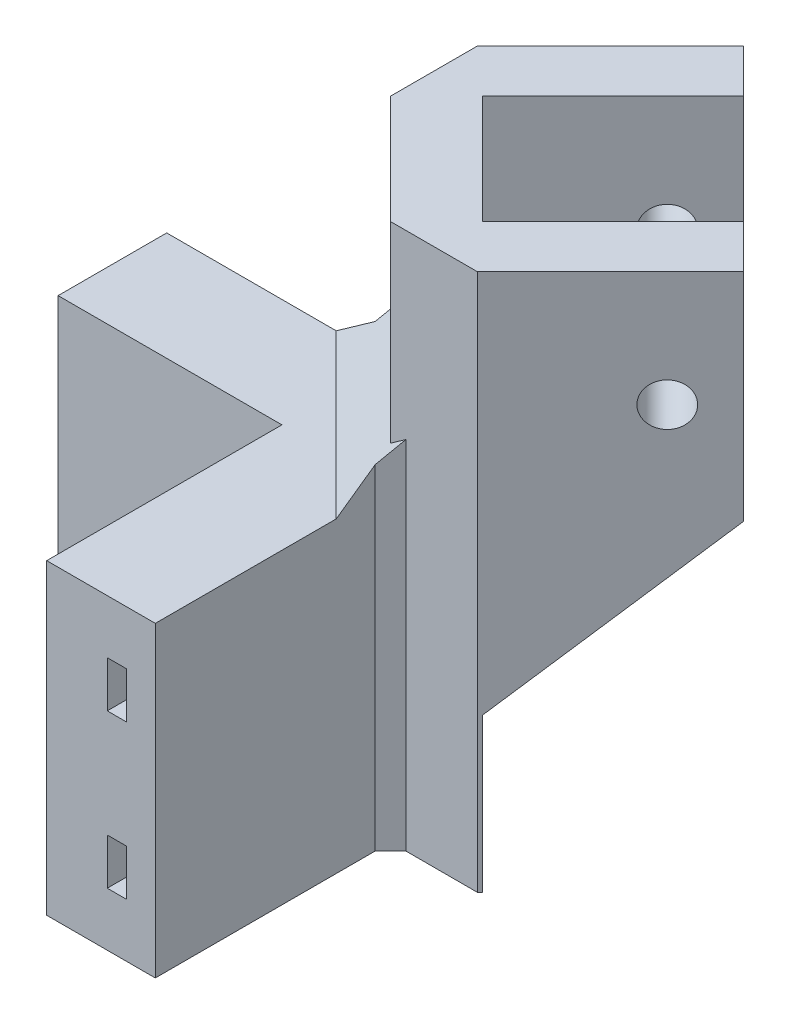
SolidWorks part; units mm, degrees
material "ABS"
ref_plane "Front Plane" through (0, 0, 0) normal (0, 0, 1) x (1, 0, 0)
ref_plane "Top Plane" through (0, 0, 0) normal (0, 1, 0) x (1, 0, 0)
ref_plane "Right Plane" through (0, 0, 0) normal (1, 0, 0) x (0, 0, -1)
sketch "Sketch1" plane through (0, 0, 0) normal (0, 1, 0) x (1, 0, 0)
  line L0 (-75, -75) -> (-25, -75) construction
  line L1 (-75, 75) -> (75, 75) construction
  line L2 (-75, 75) -> (-75, -75) construction
  line L3 (-75, -75) -> (75, -75) construction
  line L4 (75, 75) -> (75, -75) construction
  line L5 (-75, 75) -> (75, -75) construction
  line L6 (-75, -75) -> (75, 75) construction
  line L7 (-25, -75) -> (-25, -25) construction
  line L8 (-25, -25) -> (-75, -25) construction
  line L9 (-75, -25) -> (-75, -75) construction
  line L10 (-75, -60.8579) -> (-39.1421, -25) construction
  line L11 (-39.1421, -25) -> (-25, -39.1421) construction
  line L12 (-25, -39.1421) -> (-60.8579, -75) construction
  line L13 (-60.8579, -75) -> (-75, -60.8579) construction
  line L14 (-69, -54.8579) -> (-54.8579, -69)
  line L15 (-54.8579, -69) -> (-39.3015, -53.4437)
  line L23 (-53.4437, -39.3015) -> (-59.1005, -33.6447)
  line L24 (-59.1005, -33.6447) -> (-75, -49.5442)
  line L25 (-75, -49.5442) -> (-75, -75)
  line L26 (-39.3015, -53.4437) -> (-33.6447, -59.1005)
  line L27 (-33.6447, -59.1005) -> (-49.5442, -75)
  line L28 (-49.5442, -75) -> (-75, -75)
  line L29 (-69, -54.8579) -> (-53.4437, -39.3015)
  point P0 (0, 0)
  dimension "D1" = 150
  dimension "D2" = 150
  dimension "D3" = 50
  dimension "D4" = 20
  dimension "D5" = 22
  dimension "D6" = 6
  dimension "D7" = 8
extrude "Boss-Extrude1" add sketch "Sketch1" along normal blind 30 contours L27 L28 L25 L24 L23 L29 L14 L15 L26
sketch "Sketch2" plane through (12.7279, 0, 12.7279) normal (0.7071, 0, 0.7071) x (0.7071, 0, -0.7071)
  line L0 (-70.5807, 30) -> (-70.5807, 15) construction
  line L2 (-65.5807, 30) -> (-65.5807, 0) construction
  circle A0 centre (-70.5807, 15) radius 2.8
  point P4 (-88.066, 0)
  dimension "D2" = 5.6
  dimension "D1" = 15
  dimension "D3" = 5
extrude "Cut-Extrude1" cut sketch "Sketch2" against normal blind 65
sketch "Sketch4" plane through (0, 0, 0) normal (0, -1, 0) x (1, 0, 0)
  line L0 (-60.8579, 75) -> (-75, 60.8579)
  line L1 (-49.5442, 75) -> (-75, 75) construction
  line L2 (-75, 49.5442) -> (-75, 75) construction
  line L3 (-75, 60.8579) -> (-82.4343, 68.2922)
  line L4 (-82.4343, 68.2922) -> (-68.2922, 82.4343)
  line L5 (-68.2922, 82.4343) -> (-60.8579, 75)
  line L6 (-75, 75) -> (-75, 60.8579) construction
  line L7 (-75, 75) -> (-60.8579, 75) construction
  dimension "D1" = 10
extrude "Cut-Extrude2" cut sketch "Sketch4" against normal blind 65
sketch "Sketch5" plane through (0, 0, 0) normal (0, -1, 0) x (1, 0, 0)
  line L2 (-49.5442, 75) -> (-75, 75) construction
  line L3 (-75, 49.5442) -> (-75, 75) construction
  line L5 (-75, 75) -> (-116, 75) construction
  line L6 (-75, 75) -> (-75, 116) construction
  line L7 (-75, 116) -> (-116, 116) construction
  line L8 (-116, 75) -> (-116, 116) construction
  dimension "D1" = 41
  dimension "D2" = 41
sketch "Sketch6" plane through (0, 0, 0) normal (0, -1, 0) x (1, 0, 0)
  line L0 (-60.8579, 75) -> (-60.8579, 105.6326)
  line L1 (-60.8579, 105.6326) -> (-75, 105.6326)
  line L2 (-75, 75) -> (-75, 116) construction
  line L3 (-75, 105.6326) -> (-75, 75)
  line L4 (-75, 75) -> (-104.1496, 75)
  line L5 (-75, 75) -> (-116, 75) construction
  line L6 (-104.1496, 75) -> (-104.1496, 60.8579)
  line L7 (-75, 60.8579) -> (-104.1496, 60.8579)
  line L9 (-60.8579, 75) -> (-49.5442, 75)
  line L10 (-49.5442, 75) -> (-33.6447, 59.1005)
  line L11 (-33.6447, 59.1005) -> (-39.3015, 53.4437)
  line L12 (-39.3015, 53.4437) -> (-54.8579, 69)
  line L13 (-54.8579, 69) -> (-69, 54.8579)
  line L14 (-69, 54.8579) -> (-54.8579, 69) construction
  line L15 (-69, 54.8579) -> (-53.4437, 39.3015)
  line L16 (-53.4437, 39.3015) -> (-59.1005, 33.6447)
  line L17 (-59.1005, 33.6447) -> (-75, 49.5442)
  line L18 (-75, 49.5442) -> (-75, 60.8579)
extrude "Boss-Extrude2" add sketch "Sketch6" along normal blind 40
sketch "Sketch9" plane through (-61.9289, 0, 61.9289) normal (0.7071, 0, -0.7071) x (-0.7071, 0, -0.7071)
  line L0 (-27.9552, -40) -> (27.9552, -40)
  line L2 (30.6119, -40) -> (10, -40) construction
  line L3 (27.9552, -40) -> (27.9552, -20)
  line L4 (27.9552, -20) -> (-27.9552, -20)
  line L5 (-27.9552, -20) -> (-27.9552, -40)
  point P3 (0, -40)
  dimension "D1" = 20
extrude "Cut-Extrude4" cut sketch "Sketch9" along normal blind 40
sketch "Sketch10" plane through (12.7279, 0, 12.7279) normal (0.7071, 0, 0.7071) x (0.7071, 0, -0.7071)
  line L0 (-86.666, 0) -> (-65.5807, 0) construction
  line L1 (-88.066, 0) -> (-106.066, 0) construction
  line L2 (-65.5807, 30) -> (-65.5807, -20) construction
  line L3 (-87.5807, -20) -> (-65.5807, 0)
  line L4 (-65.5807, 0) -> (-65.5807, -20)
  line L5 (-65.5807, -20) -> (-87.5807, -20)
extrude "Cut-Extrude5" cut sketch "Sketch10" against normal blind 40
chamfer "Chamfer1" distance 5 angle 45 1 edges at (-67.9289, 0, 67.9289)
ref_plane "Plane2" through (0, -10, 0) normal (0, 1, 0) x (1, 0, 0)
ref_plane "Plane3" through (0, -30, 0) normal (0, 1, 0) x (1, 0, 0)
sketch "Sketch12" plane through (0, -10, 0) normal (0, 1, 0) x (1, 0, 0)
  line L0 (-75, -49.5442) -> (-75, -75) construction
  line L1 (-49.5442, -75) -> (-75, -75) construction
  line L2 (-75, -67.1145) -> (-110.7067, -67.1145)
  line L3 (-67.1145, -75) -> (-67.1145, -107.3883)
  line L4 (-75, -64.6145) -> (-110.7067, -64.6145)
  line L5 (-110.7067, -64.6145) -> (-110.7067, -67.1145)
  line L6 (-64.6145, -75) -> (-64.6145, -107.3883)
  line L7 (-64.6145, -107.3883) -> (-67.1145, -107.3883)
  arc A0 (-75, -67.1145) -> (-67.1145, -75) centre (-75, -75) cw
  arc A1 (-75, -64.6145) -> (-64.6145, -75) centre (-75, -75) cw
  dimension "D1" = 2.5
sketch "Sketch13" plane through (0, -30, 0) normal (0, 1, 0) x (1, 0, 0)
  line L6 (-110.7067, -67.1145) -> (-75, -67.1145)
  line L7 (-110.7067, -64.6145) -> (-110.7067, -67.1145)
  line L8 (-75, -64.6145) -> (-110.7067, -64.6145)
  line L9 (-64.6145, -107.3883) -> (-64.6145, -75)
  line L10 (-67.1145, -107.3883) -> (-64.6145, -107.3883)
  line L11 (-67.1145, -75) -> (-67.1145, -107.3883)
  line L12 (-110.7067, -67.1145) -> (-75, -67.1145)
  line L13 (-110.7067, -64.6145) -> (-110.7067, -67.1145)
  line L14 (-75, -64.6145) -> (-110.7067, -64.6145)
  line L15 (-64.6145, -107.3883) -> (-64.6145, -75)
  line L16 (-67.1145, -107.3883) -> (-64.6145, -107.3883)
  line L17 (-67.1145, -75) -> (-67.1145, -107.3883)
  arc A2 (-64.6145, -75) -> (-75, -64.6145) centre (-75, -75) ccw
  arc A3 (-67.1145, -75) -> (-75, -67.1145) centre (-75, -75) ccw
  arc A4 (-64.6145, -75) -> (-75, -64.6145) centre (-75, -75) ccw
  arc A5 (-67.1145, -75) -> (-75, -67.1145) centre (-75, -75) ccw
  dimension "D1" = 0
extrude "Cut-Extrude6" cut sketch "Sketch12" against normal blind 3 and the other way blind 3 contours L6 L7 L3 A0 L2 L5 L4 A1
extrude "Cut-Extrude7" cut sketch "Sketch13" against normal blind 3 and the other way blind 3 contours L17 L16 L15 A4 L14 L13 L12 A5
sketch "Sketch14" plane through (-46.3726, 0, 46.3726) normal (0.7071, 0, -0.7071) x (-0.7071, 0, -0.7071)
  line L1 (-18, 30) -> (-10, 30)
  line L2 (-18, 30) -> (-18, 0)
  line L3 (-18, 0) -> (-10, 0)
  line L4 (-10, 30) -> (-10, 0)
  line L5 (18, 30) -> (10, 30)
  line L6 (18, 30) -> (18, 0)
  line L7 (18, 0) -> (10, 0)
  line L8 (10, 30) -> (10, 0)
extrude "Boss-Extrude3" add sketch "Sketch14" along normal blind 2
sketch "Sketch15" plane through (-20.9831, 32.642, 20.9831) normal (0.4757, -0.7399, -0.4757) x (0.8796, 0.4001, 0.2572)
  line L0 (-16.6535, 59.585) -> (-53.5075, 34.6032)
  line L1 (-53.5075, 34.6032) -> (-43.1083, 19.2619)
  line L2 (-43.1083, 19.2619) -> (-6.2543, 44.2436)
  line L3 (-6.2543, 44.2436) -> (-16.6535, 59.585)
extrude "Cut-Extrude8" cut sketch "Sketch15" along normal blind 22
chamfer "Chamfer2" distance 2 angle 45 2 edges at (-75, -17.5, 60.8579) (-60.8579, -17.5, 75)
sketch "Sketch17" plane through (12.7279, 0, 12.7279) normal (0.7071, 0, 0.7071) x (0.7071, 0, -0.7071)
  line L0 (-70.5807, 15) -> (-70.5807, 30) construction
  line L1 (-63.5807, 30) -> (-88.066, 30) construction
sketch "Sketch16" plane through (0, 0, 0) normal (0, 1, 0) x (1, 0, 0)
  line L0 (-116, -75) -> (-75, -116) construction
  line L1 (-37.1939, -62.6498) -> (-56.9929, -42.8508) construction
  line L2 (-32.2304, -57.6863) -> (-49.5442, -75) construction
  line L3 (-69, -54.8579) -> (-52.0294, -37.8873) construction
  line L4 (-75, -75) -> (-49.9219, -49.9219) construction
  dimension "D1" = 25.0781
